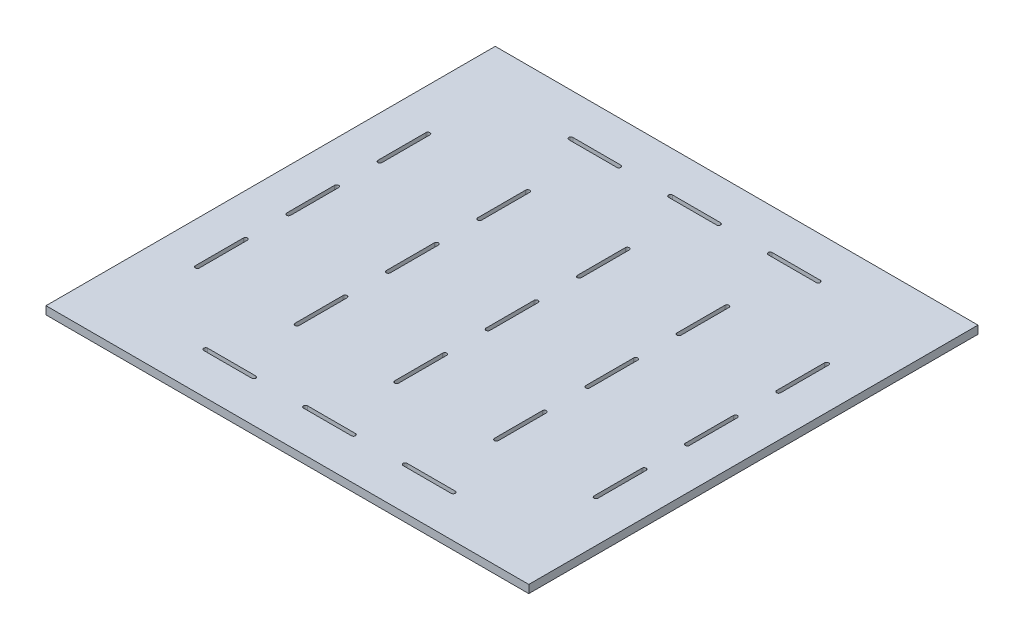
SolidWorks part; units mm, degrees
material "6061-T6 (SS)"
ref_plane "Front Plane" through (0, 0, 0) normal (0, 0, 1) x (1, 0, 0)
ref_plane "Top Plane" through (0, 0, 0) normal (0, 1, 0) x (1, 0, 0)
ref_plane "Right Plane" through (0, 0, 0) normal (1, 0, 0) x (0, 0, -1)
sketch "Sketch1" plane through (0, 0, 0) normal (0, 1, 0) x (1, 0, 0)
  line L0 (316.1, 289.475) -> (237.075, 289.475) construction
  line L1 (237.075, 289.475) -> (158.05, 289.475) construction
  line L2 (79.025, 0) -> (158.05, 0) construction
  line L3 (158.05, 0) -> (237.075, 0) construction
  line L4 (237.075, 0) -> (316.1, 0) construction
  line L5 (316.1, 0) -> (316.1, 289.475) construction
  line L6 (237.075, 0) -> (237.075, 289.475) construction
  line L7 (158.05, 0) -> (158.05, 289.475) construction
  line L8 (158.05, 289.475) -> (79.025, 289.475) construction
  line L9 (79.025, 289.475) -> (0, 289.475) construction
  line L10 (79.025, 289.475) -> (79.025, 217.1063) construction
  line L11 (79.025, 217.1063) -> (79.025, 144.7375) construction
  line L12 (79.025, 144.7375) -> (79.025, 72.3688) construction
  line L13 (79.025, 72.3688) -> (79.025, 0) construction
  line L14 (0, 0) -> (0, 289.475) construction
  line L15 (0, 0) -> (79.025, 0) construction
  line L16 (316.1, 289.475) -> (237.075, 289.475) construction
  line L17 (237.075, 289.475) -> (158.05, 289.475) construction
  line L18 (79.025, 0) -> (158.05, 0) construction
  line L19 (158.05, 0) -> (237.075, 0) construction
  line L20 (237.075, 0) -> (316.1, 0) construction
  line L21 (316.1, 0) -> (316.1, 289.475) construction
  line L22 (237.075, 0) -> (237.075, 289.475) construction
  line L23 (158.05, 0) -> (158.05, 289.475) construction
  line L24 (158.05, 289.475) -> (79.025, 289.475) construction
  line L25 (79.025, 289.475) -> (0, 289.475) construction
  line L26 (79.025, 289.475) -> (79.025, 217.1063) construction
  line L27 (79.025, 217.1063) -> (79.025, 144.7375) construction
  line L28 (79.025, 144.7375) -> (79.025, 72.3688) construction
  line L29 (79.025, 72.3688) -> (79.025, 0) construction
  line L30 (0, 0) -> (0, 289.475) construction
  line L31 (0, 0) -> (79.025, 0) construction
  line L32 (349.4375, 322.8125) -> (349.4375, -33.3375)
  line L33 (-33.3375, 322.8125) -> (349.4375, 322.8125)
  line L34 (-33.3375, 322.8125) -> (-33.3375, -33.3375)
  line L35 (-33.3375, 144.7375) -> (158.05, 144.7375) construction
  line L36 (158.05, 322.8125) -> (158.05, 144.7375) construction
  line L37 (-33.3375, -33.3375) -> (349.4375, -33.3375)
  line L38 (0, 0) -> (-25.4, 0) construction
  line L39 (-25.4, 0) -> (-25.4, 289.475) construction
  line L40 (0, 289.475) -> (-25.4, 289.475) construction
  line L41 (0, 0) -> (-25.4, 0) construction
  line L42 (-25.4, 0) -> (-25.4, 289.475) construction
  line L43 (0, 289.475) -> (-25.4, 289.475) construction
  point P0 (158.05, 217.1063)
  point P2 (158.05, 144.7375)
  point P4 (158.05, 72.3688)
  point P6 (237.075, 72.3688)
  point P8 (237.075, 144.7375)
  point P10 (237.075, 217.1063)
  point P36 (349.4375, 144.7375)
  dimension "D1" = 33.3375
  dimension "D2" = 7.9375
extrude "Boss-Extrude1" add sketch "Sketch1" along normal mid plane 6.35
sketch "Sketch3" plane through (0, -3.175, 0) normal (0, 1, 0) x (1, 0, 0)
  line L0 (314.5125, 53.3188) -> (314.5125, 91.4188)
  line L1 (-1.5875, 53.3188) -> (1.5875, 53.3188) construction
  line L2 (-1.5875, 53.3188) -> (-1.5875, 91.4188)
  line L3 (-1.5875, 91.4188) -> (1.5875, 91.4188) construction
  line L4 (1.5875, 53.3188) -> (1.5875, 91.4188)
  line L5 (-1.5875, 53.3188) -> (1.5875, 91.4188) construction
  line L6 (-1.5875, 91.4188) -> (1.5875, 53.3188) construction
  line L7 (317.6875, 53.3188) -> (317.6875, 91.4188)
  line L8 (314.5125, 53.3188) -> (317.6875, 53.3188) construction
  line L9 (314.5125, 91.4188) -> (317.6875, 91.4188) construction
  line L10 (314.5125, 53.3188) -> (317.6875, 91.4188) construction
  line L11 (314.5125, 91.4188) -> (317.6875, 53.3188) construction
  line L12 (314.5125, 125.6875) -> (314.5125, 163.7875)
  line L13 (317.6875, 125.6875) -> (317.6875, 163.7875)
  line L14 (314.5125, 125.6875) -> (317.6875, 125.6875) construction
  line L15 (314.5125, 163.7875) -> (317.6875, 163.7875) construction
  line L16 (314.5125, 125.6875) -> (317.6875, 163.7875) construction
  line L17 (314.5125, 163.7875) -> (317.6875, 125.6875) construction
  line L18 (314.5125, 198.0563) -> (314.5125, 236.1563)
  line L19 (317.6875, 198.0563) -> (317.6875, 236.1563)
  line L20 (314.5125, 198.0563) -> (317.6875, 198.0563) construction
  line L21 (314.5125, 236.1563) -> (317.6875, 236.1563) construction
  line L22 (314.5125, 198.0563) -> (317.6875, 236.1563) construction
  line L23 (314.5125, 236.1563) -> (317.6875, 198.0563) construction
  line L24 (-1.5875, 125.6875) -> (-1.5875, 163.7875)
  line L25 (1.5875, 125.6875) -> (1.5875, 163.7875)
  line L26 (-1.5875, 125.6875) -> (1.5875, 125.6875) construction
  line L27 (-1.5875, 163.7875) -> (1.5875, 163.7875) construction
  line L28 (-1.5875, 125.6875) -> (1.5875, 163.7875) construction
  line L29 (-1.5875, 163.7875) -> (1.5875, 125.6875) construction
  line L30 (-1.5875, 198.0563) -> (-1.5875, 236.1563)
  line L31 (1.5875, 198.0563) -> (1.5875, 236.1563)
  line L32 (-1.5875, 198.0563) -> (1.5875, 198.0563) construction
  line L33 (-1.5875, 236.1563) -> (1.5875, 236.1563) construction
  line L34 (-1.5875, 198.0563) -> (1.5875, 236.1563) construction
  line L35 (-1.5875, 236.1563) -> (1.5875, 198.0563) construction
  arc A0 (-1.5875, 53.3188) -> (1.5875, 53.3188) centre (0, 53.3188) ccw
  arc A1 (-1.5875, 91.4188) -> (1.5875, 91.4188) centre (0, 91.4188) cw
  arc A2 (314.5125, 53.3188) -> (317.6875, 53.3188) centre (316.1, 53.3188) ccw
  arc A3 (314.5125, 91.4188) -> (317.6875, 91.4188) centre (316.1, 91.4188) cw
  arc A4 (314.5125, 125.6875) -> (317.6875, 125.6875) centre (316.1, 125.6875) ccw
  arc A5 (314.5125, 163.7875) -> (317.6875, 163.7875) centre (316.1, 163.7875) cw
  arc A6 (314.5125, 198.0563) -> (317.6875, 198.0563) centre (316.1, 198.0563) ccw
  arc A7 (314.5125, 236.1563) -> (317.6875, 236.1563) centre (316.1, 236.1563) cw
  arc A8 (-1.5875, 125.6875) -> (1.5875, 125.6875) centre (0, 125.6875) ccw
  arc A9 (-1.5875, 163.7875) -> (1.5875, 163.7875) centre (0, 163.7875) cw
  arc A10 (-1.5875, 198.0563) -> (1.5875, 198.0563) centre (0, 198.0563) ccw
  arc A11 (-1.5875, 236.1563) -> (1.5875, 236.1563) centre (0, 236.1563) cw
  point P0 (0, 72.3688)
  point P4 (0, 217.1063)
  point P6 (316.1, 72.3688)
  point P8 (0, 72.3688)
  point P17 (316.1, 72.3688)
  point P19 (316.1, 72.3688)
  point P25 (316.1, 144.7375)
  point P27 (316.1, 144.7375)
  point P33 (316.1, 217.1063)
  point P35 (316.1, 217.1063)
  point P41 (0, 144.7375)
  point P43 (0, 144.7375)
  point P49 (0, 217.1063)
  point P51 (0, 217.1063)
  dimension "D1" = 38.1
  dimension "D2" = 3.175
  dimension "D4" = 2
  dimension "D3" = 3
extrude "Outer Side Wall Weld Tab Cutouts" cut sketch "Sketch3" along normal up to surface (6.35 mm away) up to face at (158.05, 3.175, -144.7375)
sketch "Sketch4" plane through (0, -3.175, 0) normal (0, 1, 0) x (1, 0, 0)
  line L0 (156.4625, 53.3188) -> (156.4625, 91.4188)
  line L1 (77.4375, 53.3188) -> (80.6125, 53.3188) construction
  line L2 (77.4375, 53.3188) -> (77.4375, 91.4188)
  line L3 (77.4375, 91.4188) -> (80.6125, 91.4188) construction
  line L4 (80.6125, 53.3188) -> (80.6125, 91.4188)
  line L5 (77.4375, 53.3188) -> (80.6125, 91.4188) construction
  line L6 (77.4375, 91.4188) -> (80.6125, 53.3188) construction
  line L7 (159.6375, 53.3188) -> (159.6375, 91.4188)
  line L8 (156.4625, 53.3188) -> (159.6375, 53.3188) construction
  line L9 (156.4625, 91.4188) -> (159.6375, 91.4188) construction
  line L10 (156.4625, 53.3188) -> (159.6375, 91.4188) construction
  line L11 (156.4625, 91.4188) -> (159.6375, 53.3188) construction
  line L12 (235.4875, 53.3188) -> (235.4875, 91.4188)
  line L13 (238.6625, 53.3188) -> (238.6625, 91.4188)
  line L14 (235.4875, 53.3188) -> (238.6625, 53.3188) construction
  line L15 (235.4875, 91.4188) -> (238.6625, 91.4188) construction
  line L16 (235.4875, 53.3188) -> (238.6625, 91.4188) construction
  line L17 (235.4875, 91.4188) -> (238.6625, 53.3188) construction
  line L18 (156.4625, 125.6875) -> (156.4625, 163.7875)
  line L19 (159.6375, 125.6875) -> (159.6375, 163.7875)
  line L20 (156.4625, 125.6875) -> (159.6375, 125.6875) construction
  line L21 (156.4625, 163.7875) -> (159.6375, 163.7875) construction
  line L22 (156.4625, 125.6875) -> (159.6375, 163.7875) construction
  line L23 (156.4625, 163.7875) -> (159.6375, 125.6875) construction
  line L24 (235.4875, 125.6875) -> (235.4875, 163.7875)
  line L25 (238.6625, 125.6875) -> (238.6625, 163.7875)
  line L26 (235.4875, 125.6875) -> (238.6625, 125.6875) construction
  line L27 (235.4875, 163.7875) -> (238.6625, 163.7875) construction
  line L28 (235.4875, 125.6875) -> (238.6625, 163.7875) construction
  line L29 (235.4875, 163.7875) -> (238.6625, 125.6875) construction
  line L30 (156.4625, 198.0563) -> (156.4625, 236.1563)
  line L31 (159.6375, 198.0563) -> (159.6375, 236.1563)
  line L32 (156.4625, 198.0563) -> (159.6375, 198.0563) construction
  line L33 (156.4625, 236.1563) -> (159.6375, 236.1563) construction
  line L34 (156.4625, 198.0563) -> (159.6375, 236.1563) construction
  line L35 (156.4625, 236.1563) -> (159.6375, 198.0563) construction
  line L36 (235.4875, 198.0563) -> (235.4875, 236.1563)
  line L37 (238.6625, 198.0563) -> (238.6625, 236.1563)
  line L38 (235.4875, 198.0563) -> (238.6625, 198.0563) construction
  line L39 (235.4875, 236.1563) -> (238.6625, 236.1563) construction
  line L40 (235.4875, 198.0563) -> (238.6625, 236.1563) construction
  line L41 (235.4875, 236.1563) -> (238.6625, 198.0563) construction
  line L42 (77.4375, 125.6875) -> (77.4375, 163.7875)
  line L43 (80.6125, 125.6875) -> (80.6125, 163.7875)
  line L44 (77.4375, 125.6875) -> (80.6125, 125.6875) construction
  line L45 (77.4375, 163.7875) -> (80.6125, 163.7875) construction
  line L46 (77.4375, 125.6875) -> (80.6125, 163.7875) construction
  line L47 (77.4375, 163.7875) -> (80.6125, 125.6875) construction
  line L48 (77.4375, 198.0563) -> (77.4375, 236.1563)
  line L49 (80.6125, 198.0563) -> (80.6125, 236.1563)
  line L50 (77.4375, 198.0563) -> (80.6125, 198.0563) construction
  line L51 (77.4375, 236.1563) -> (80.6125, 236.1563) construction
  line L52 (77.4375, 198.0563) -> (80.6125, 236.1563) construction
  line L53 (77.4375, 236.1563) -> (80.6125, 198.0563) construction
  arc A0 (77.4375, 53.3188) -> (80.6125, 53.3188) centre (79.025, 53.3188) ccw
  arc A1 (77.4375, 91.4188) -> (80.6125, 91.4188) centre (79.025, 91.4188) cw
  arc A2 (156.4625, 53.3188) -> (159.6375, 53.3188) centre (158.05, 53.3188) ccw
  arc A3 (156.4625, 91.4188) -> (159.6375, 91.4188) centre (158.05, 91.4188) cw
  arc A4 (235.4875, 53.3188) -> (238.6625, 53.3188) centre (237.075, 53.3188) ccw
  arc A5 (235.4875, 91.4188) -> (238.6625, 91.4188) centre (237.075, 91.4188) cw
  arc A6 (156.4625, 125.6875) -> (159.6375, 125.6875) centre (158.05, 125.6875) ccw
  arc A7 (156.4625, 163.7875) -> (159.6375, 163.7875) centre (158.05, 163.7875) cw
  arc A8 (235.4875, 125.6875) -> (238.6625, 125.6875) centre (237.075, 125.6875) ccw
  arc A9 (235.4875, 163.7875) -> (238.6625, 163.7875) centre (237.075, 163.7875) cw
  arc A10 (156.4625, 198.0563) -> (159.6375, 198.0563) centre (158.05, 198.0563) ccw
  arc A11 (156.4625, 236.1563) -> (159.6375, 236.1563) centre (158.05, 236.1563) cw
  arc A12 (235.4875, 198.0563) -> (238.6625, 198.0563) centre (237.075, 198.0563) ccw
  arc A13 (235.4875, 236.1563) -> (238.6625, 236.1563) centre (237.075, 236.1563) cw
  arc A14 (77.4375, 125.6875) -> (80.6125, 125.6875) centre (79.025, 125.6875) ccw
  arc A15 (77.4375, 163.7875) -> (80.6125, 163.7875) centre (79.025, 163.7875) cw
  arc A16 (77.4375, 198.0563) -> (80.6125, 198.0563) centre (79.025, 198.0563) ccw
  arc A17 (77.4375, 236.1563) -> (80.6125, 236.1563) centre (79.025, 236.1563) cw
  point P0 (79.025, 217.1063)
  point P2 (237.075, 72.3688)
  point P4 (79.025, 72.3688)
  point P6 (79.025, 72.3688)
  point P17 (158.05, 72.3688)
  point P18 (158.05, 72.3688)
  point P26 (237.075, 72.3688)
  point P27 (237.075, 72.3688)
  point P35 (158.05, 144.7375)
  point P36 (158.05, 144.7375)
  point P44 (237.075, 144.7375)
  point P45 (237.075, 144.7375)
  point P53 (158.05, 217.1063)
  point P54 (158.05, 217.1063)
  point P62 (237.075, 217.1063)
  point P63 (237.075, 217.1063)
  point P71 (79.025, 144.7375)
  point P72 (79.025, 144.7375)
  point P80 (79.025, 217.1063)
  point P81 (79.025, 217.1063)
  dimension "D3" = 3
  dimension "D1" = 3.175
  dimension "D2" = 38.1
  dimension "D4" = 3
extrude "Cut-Extrude2" cut sketch "Sketch4" along normal up to surface (6.35 mm away) up to face at (158.05, 3.175, -144.7375)
sketch "Sketch5" plane through (0, -3.175, 0) normal (0, 1, 0) x (1, 0, 0)
  line L0 (139, 1.5875) -> (177.1, 1.5875)
  line L1 (59.975, 1.5875) -> (98.075, 1.5875)
  line L2 (59.975, 1.5875) -> (59.975, -1.5875) construction
  line L3 (59.975, -1.5875) -> (98.075, -1.5875)
  line L4 (98.075, 1.5875) -> (98.075, -1.5875) construction
  line L5 (59.975, 1.5875) -> (98.075, -1.5875) construction
  line L6 (59.975, -1.5875) -> (98.075, 1.5875) construction
  line L7 (139, -1.5875) -> (177.1, -1.5875)
  line L8 (139, 1.5875) -> (139, -1.5875) construction
  line L9 (177.1, 1.5875) -> (177.1, -1.5875) construction
  line L10 (139, 1.5875) -> (177.1, -1.5875) construction
  line L11 (139, -1.5875) -> (177.1, 1.5875) construction
  line L12 (218.025, 1.5875) -> (256.125, 1.5875)
  line L13 (218.025, -1.5875) -> (256.125, -1.5875)
  line L14 (218.025, 1.5875) -> (218.025, -1.5875) construction
  line L15 (256.125, 1.5875) -> (256.125, -1.5875) construction
  line L16 (218.025, 1.5875) -> (256.125, -1.5875) construction
  line L17 (218.025, -1.5875) -> (256.125, 1.5875) construction
  line L18 (139, 291.0625) -> (177.1, 291.0625)
  line L19 (139, 287.8875) -> (177.1, 287.8875)
  line L20 (139, 291.0625) -> (139, 287.8875) construction
  line L21 (177.1, 291.0625) -> (177.1, 287.8875) construction
  line L22 (139, 291.0625) -> (177.1, 287.8875) construction
  line L23 (139, 287.8875) -> (177.1, 291.0625) construction
  line L24 (218.025, 291.0625) -> (256.125, 291.0625)
  line L25 (218.025, 287.8875) -> (256.125, 287.8875)
  line L26 (218.025, 291.0625) -> (218.025, 287.8875) construction
  line L27 (256.125, 291.0625) -> (256.125, 287.8875) construction
  line L28 (218.025, 291.0625) -> (256.125, 287.8875) construction
  line L29 (218.025, 287.8875) -> (256.125, 291.0625) construction
  line L30 (59.975, 291.0625) -> (98.075, 291.0625)
  line L31 (59.975, 287.8875) -> (98.075, 287.8875)
  line L32 (59.975, 291.0625) -> (59.975, 287.8875) construction
  line L33 (98.075, 291.0625) -> (98.075, 287.8875) construction
  line L34 (59.975, 291.0625) -> (98.075, 287.8875) construction
  line L35 (59.975, 287.8875) -> (98.075, 291.0625) construction
  arc A0 (59.975, 1.5875) -> (59.975, -1.5875) centre (59.975, 0) ccw
  arc A1 (98.075, -1.5875) -> (98.075, 1.5875) centre (98.075, 0) ccw
  arc A2 (139, 1.5875) -> (139, -1.5875) centre (139, 0) ccw
  arc A3 (177.1, -1.5875) -> (177.1, 1.5875) centre (177.1, 0) ccw
  arc A4 (218.025, 1.5875) -> (218.025, -1.5875) centre (218.025, 0) ccw
  arc A5 (256.125, -1.5875) -> (256.125, 1.5875) centre (256.125, 0) ccw
  arc A6 (139, 291.0625) -> (139, 287.8875) centre (139, 289.475) ccw
  arc A7 (177.1, 287.8875) -> (177.1, 291.0625) centre (177.1, 289.475) ccw
  arc A8 (218.025, 291.0625) -> (218.025, 287.8875) centre (218.025, 289.475) ccw
  arc A9 (256.125, 287.8875) -> (256.125, 291.0625) centre (256.125, 289.475) ccw
  arc A10 (59.975, 291.0625) -> (59.975, 287.8875) centre (59.975, 289.475) ccw
  arc A11 (98.075, 287.8875) -> (98.075, 291.0625) centre (98.075, 289.475) ccw
  point P0 (79.025, 289.475)
  point P2 (237.075, 0)
  point P4 (79.025, 0)
  point P6 (79.025, 0)
  point P16 (158.05, 0)
  point P17 (158.05, 0)
  point P24 (237.075, 0)
  point P25 (237.075, 0)
  point P32 (158.05, 289.475)
  point P33 (158.05, 289.475)
  point P40 (237.075, 289.475)
  point P41 (237.075, 289.475)
  point P48 (79.025, 289.475)
  point P49 (79.025, 289.475)
  dimension "D1" = 3.175
  dimension "D2" = 38.1
  dimension "D4" = 3
  dimension "D3" = 2
extrude "Cut-Extrude3" cut sketch "Sketch5" along normal up to surface (6.35 mm away) up to face at (158.05, 3.175, -144.7375)
equation "\"D1@Boss-Extrude1\"=\"acc bottom wall thickness@FS2-EN-ACC-A-0003-V1, ACCUMULATOR CONTAINER.Assembly\""
equation "\"D1@Sketch1\"=\"acc mounting flange width@FS2-EN-ACC-A-0003-V1, ACCUMULATOR CONTAINER.Assembly\"+\"weld beam width@FS2-EN-ACC-A-0003-V1, ACCUMULATOR CONTAINER.Assembly\"+\"acc rear wall thickness@FS2-EN-ACC-A-0003-V1, ACCUMULATOR CONTAINER.Assembly\"/2"
equation "\"D1@Sketch3\"=\"weld slot length@FS2-EN-ACC-A-0003-V1, ACCUMULATOR CONTAINER.Assembly\""
equation "\"D2@Sketch3\"=\"acc side wall thickness@FS2-EN-ACC-A-0003-V1, ACCUMULATOR CONTAINER.Assembly\""
equation "\"D1@Sketch4\"=\"acc segment side wall thickness@FS2-EN-ACC-A-0003-V1, ACCUMULATOR CONTAINER.Assembly\""
equation "\"D2@Sketch4\"=\"weld slot length@FS2-EN-ACC-A-0003-V1, ACCUMULATOR CONTAINER.Assembly\""
equation "\"D1@Sketch5\"=\"acc rear wall thickness@FS2-EN-ACC-A-0003-V1, ACCUMULATOR CONTAINER.Assembly\""
equation "\"D2@Sketch5\"=\"weld slot length@FS2-EN-ACC-A-0003-V1, ACCUMULATOR CONTAINER.Assembly\""
equation "\"D2@Sketch1\"=\"acc side wall thickness@FS2-EN-ACC-A-0003-V1, ACCUMULATOR CONTAINER.Assembly\"/2+\"weld beam width@FS2-EN-ACC-A-0003-V1, ACCUMULATOR CONTAINER.Assembly\""
